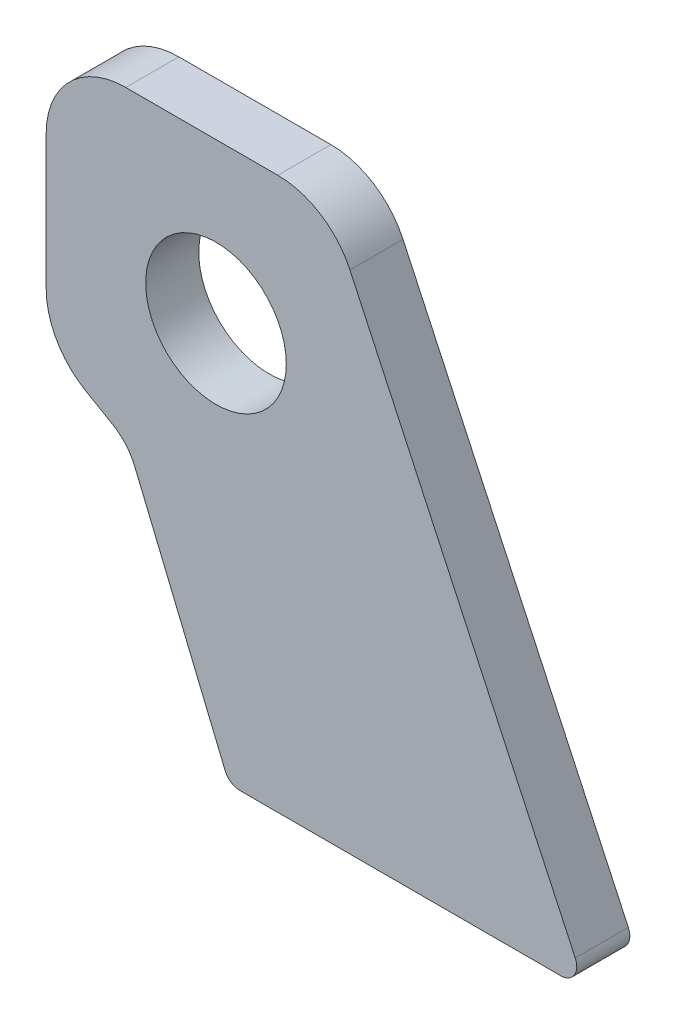
SolidWorks part; units mm, degrees
ref_plane "Plane1" through (0, 0, 0) normal (0, 0, 1) x (1, 0, 0)
ref_plane "Plane2" through (0, 0, 0) normal (0, 1, 0) x (1, 0, 0)
ref_plane "Plane3" through (0, 0, 0) normal (1, 0, 0) x (0, 0, -1)
sketch "Sketch1" plane through (0, 0, 0) normal (0, 0, 1) x (1, 0, 0)
  line L0 (-17, 30) -> (11.657, 30)
  line L2 (25.2516, 21.3393) -> (67.7189, -69.7321)
  line L3 (-19.5383, -26.1948) -> (-24.5, -23.3301)
  line L8 (65, -74) -> (4.5045, -74)
  line L10 (1.7329, -72.1481) -> (-15.2995, -31.0282)
  line L11 (-32, -10.3397) -> (-32, 15)
  circle A0 centre (0, 0) radius 13.25
  arc A1 (-17, 30) -> (-32, 15) centre (-17, 15) ccw
  arc A2 (11.657, 30) -> (25.2516, 21.3393) centre (11.657, 15) cw
  arc A3 (67.7189, -69.7321) -> (65, -74) centre (65, -71) cw
  arc A4 (4.5045, -74) -> (1.7329, -72.1481) centre (4.5045, -71) cw
  arc A5 (-19.5383, -26.1948) -> (-15.2995, -31.0282) centre (-24.5383, -34.855) cw
  arc A7 (-24.5, -23.3301) -> (-32, -10.3397) centre (-17, -10.3397) cw
  point P24 (-32, -19)
  point P26 (2.5, -74)
  dimension "D2" = 10
  dimension "D3" = 26.5
  dimension "D8" = 15
  dimension "D12" = 3
  dimension "D15" = 49
  dimension "D18" = 65.5
  dimension "D19" = 15
  dimension "D4" = 32
  dimension "D5" = 30
  dimension "D6" = 65
  dimension "D7" = 74
  dimension "D9" = 2.5
  dimension "D16" = 60
  dimension "D17" = 100
extrude "Extrude1" add sketch "Sketch1" along normal blind 10
